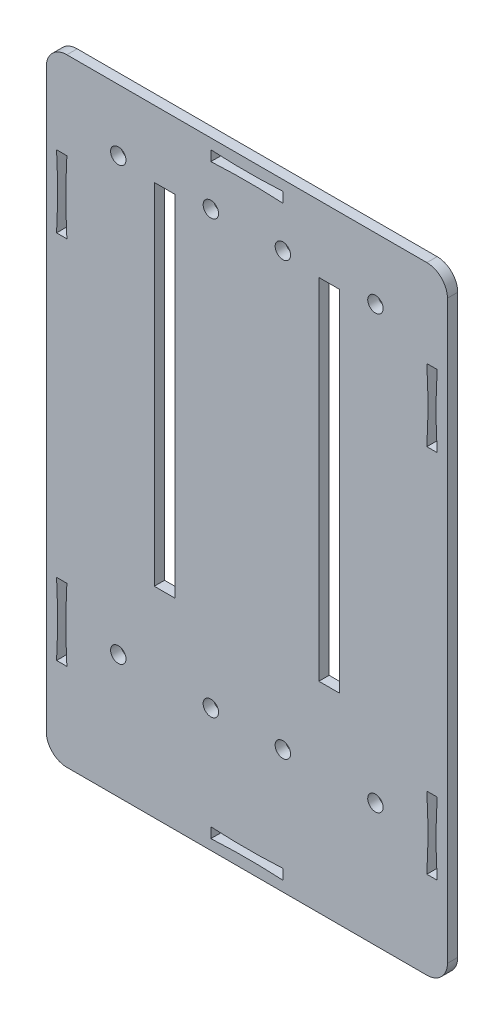
SolidWorks part; units mm, degrees
material "Acrylic (Medium-high impact)"
ref_plane "Front Plane" through (0, 0, 0) normal (0, 0, 1) x (1, 0, 0)
ref_plane "Top Plane" through (0, 0, 0) normal (0, 1, 0) x (1, 0, 0)
ref_plane "Right Plane" through (0, 0, 0) normal (1, 0, 0) x (0, 0, -1)
sketch "Sketch1" plane through (0, 0, 0) normal (0, 0, 1) x (1, 0, 0)
  line L0 (23, 107) -> (23, 39) construction
  line L1 (0, 0) -> (78, 0)
  line L2 (0, 0) -> (0, 120)
  line L3 (0, 120) -> (78, 120)
  line L4 (78, 0) -> (78, 120)
  line L5 (21, 107) -> (25, 107)
  line L6 (21, 107) -> (21, 39)
  line L7 (21, 39) -> (25, 39)
  line L8 (25, 107) -> (25, 39)
  line L9 (53, 107) -> (57, 107)
  line L10 (53, 107) -> (53, 39)
  line L11 (53, 39) -> (57, 39)
  line L12 (57, 107) -> (57, 39)
  line L13 (55, 39) -> (55, 107) construction
  line L14 (0, 60) -> (78, 60) construction
  line L15 (10, 20) -> (36, 20) construction
  line L16 (10, 20) -> (10, 112) construction
  line L17 (10, 112) -> (36, 112) construction
  line L18 (36, 20) -> (36, 112) construction
  line L19 (42, 20) -> (68, 20) construction
  line L20 (42, 20) -> (42, 112) construction
  line L21 (42, 112) -> (68, 112) construction
  line L22 (68, 20) -> (68, 112) construction
  line L23 (32, 118) -> (46, 118) construction
  line L24 (32, 118) -> (32, 116)
  line L25 (32, 116) -> (46, 116) construction
  line L26 (46, 118) -> (46, 116)
  line L27 (32, 118) -> (46, 116) construction
  line L28 (32, 116) -> (46, 118) construction
  line L29 (39, 60) -> (39, 120) construction
  line L30 (32, 4) -> (46, 2) construction
  line L31 (32, 2) -> (46, 4) construction
  line L32 (46, 2) -> (46, 4)
  line L33 (32, 4) -> (46, 4) construction
  line L34 (32, 2) -> (32, 4)
  line L35 (32, 2) -> (46, 2) construction
  line L36 (0, 0) -> (78, 0)
  line L37 (39, 60) -> (39, 0) construction
  line L38 (2, 31) -> (4, 31)
  line L39 (2, 31) -> (2, 17) construction
  line L40 (2, 17) -> (4, 17)
  line L41 (4, 31) -> (4, 17) construction
  line L42 (2, 31) -> (4, 17) construction
  line L43 (2, 17) -> (4, 31) construction
  line L44 (76, 17) -> (74, 31) construction
  line L45 (76, 31) -> (74, 17) construction
  line L46 (74, 31) -> (74, 17) construction
  line L47 (76, 17) -> (74, 17)
  line L48 (76, 31) -> (76, 17) construction
  line L49 (76, 31) -> (74, 31)
  line L50 (76, 89) -> (74, 103) construction
  line L51 (76, 103) -> (74, 89) construction
  line L52 (76, 89) -> (74, 89)
  line L53 (76, 89) -> (76, 103) construction
  line L54 (76, 103) -> (74, 103)
  line L55 (74, 89) -> (74, 103) construction
  line L56 (2, 103) -> (4, 89) construction
  line L57 (2, 89) -> (4, 103) construction
  line L58 (4, 89) -> (4, 103) construction
  line L59 (2, 103) -> (4, 103)
  line L60 (2, 89) -> (2, 103) construction
  line L61 (2, 89) -> (4, 89)
  line L62 (2, 96) -> (2.2, 96) construction
  line L63 (4, 96) -> (3.8, 96) construction
  line L64 (39, 118) -> (39, 117.8) construction
  line L65 (39, 116) -> (39, 116.2) construction
  circle A0 centre (14, 108) radius 1.5
  circle A1 centre (32, 108) radius 1.5
  circle A2 centre (14, 24) radius 1.5
  circle A3 centre (32, 24) radius 1.5
  circle A4 centre (46, 108) radius 1.5
  circle A5 centre (64, 108) radius 1.5
  circle A6 centre (46, 24) radius 1.5
  circle A7 centre (64, 24) radius 1.5
  circle A8 centre (14, 108) radius 4 construction
  circle A9 centre (32, 108) radius 4 construction
  circle A10 centre (46, 108) radius 4 construction
  circle A11 centre (64, 108) radius 4 construction
  circle A12 centre (32, 24) radius 4 construction
  spline S0 degree 2 poles (2, 103) (2.4, 96) (2, 89) knots 0 0 0 1 1 1
  spline S1 degree 2 poles (4, 103) (3.6, 96) (4, 89) knots 0 0 0 1 1 1
  spline S2 degree 2 poles (4, 17) (3.6, 24) (4, 31) knots 0 0 0 1 1 1
  spline S3 degree 2 poles (2, 17) (2.4, 24) (2, 31) knots 0 0 0 1 1 1
  spline S4 degree 2 poles (74, 17) (74.4, 24) (74, 31) knots 0 0 0 1 1 1
  spline S5 degree 2 poles (76, 17) (75.6, 24) (76, 31) knots 0 0 0 1 1 1
  spline S6 degree 2 poles (74, 103) (74.4, 96) (74, 89) knots 0 0 0 1 1 1
  spline S7 degree 2 poles (76, 103) (75.6, 96) (76, 89) knots 0 0 0 1 1 1
  spline S8 degree 2 poles (32, 118) (39, 117.6) (46, 118) knots 0 0 0 1 1 1
  spline S9 degree 2 poles (32, 116) (39, 116.4) (46, 116) knots 0 0 0 1 1 1
  spline S10 degree 2 poles (32, 4) (39, 3.6) (46, 4) knots 0 0 0 1 1 1
  spline S11 degree 2 poles (32, 2) (39, 2.4) (46, 2) knots 0 0 0 1 1 1
  point P46 (39, 117)
  point P59 (39, 3)
  point P60 (3, 24)
  point P70 (75, 24)
  point P75 (75, 96)
  point P80 (3, 96)
  dimension "D1" = 3
  dimension "D15" = 8
  dimension "D2" = 4
  dimension "D3" = 9
  dimension "D4" = 9
  dimension "D5" = 84
  dimension "D6" = 120
  dimension "D7" = 68
  dimension "D8" = 15
  dimension "D9" = 9
  dimension "D10" = 9
  dimension "D11" = 32
  dimension "D12" = 14
  dimension "D13" = 24
  dimension "D14" = 14
  dimension "D16" = 2
  dimension "D17" = 2
  dimension "D18" = 14
  dimension "D19" = 2
  dimension "D20" = 0.2
extrude "Main Slider Top" add sketch "Sketch1" along normal blind 2 contours L1 L4 L3 L2 A7 A6 A5 A4 A3 A2 A1 A0 L61 L60 L59 L58 L38 L41 L40 L39 L35 L34 L33 L32 L9 L12 L11 L10 L5 L8 L7 L6 L23 L26 L25 L24
fillet "Slide Top Contouring" radius 4 4 edges at (78, 0, 1) (0, 0, 1) (0, 120, 1) (78, 120, 1)
